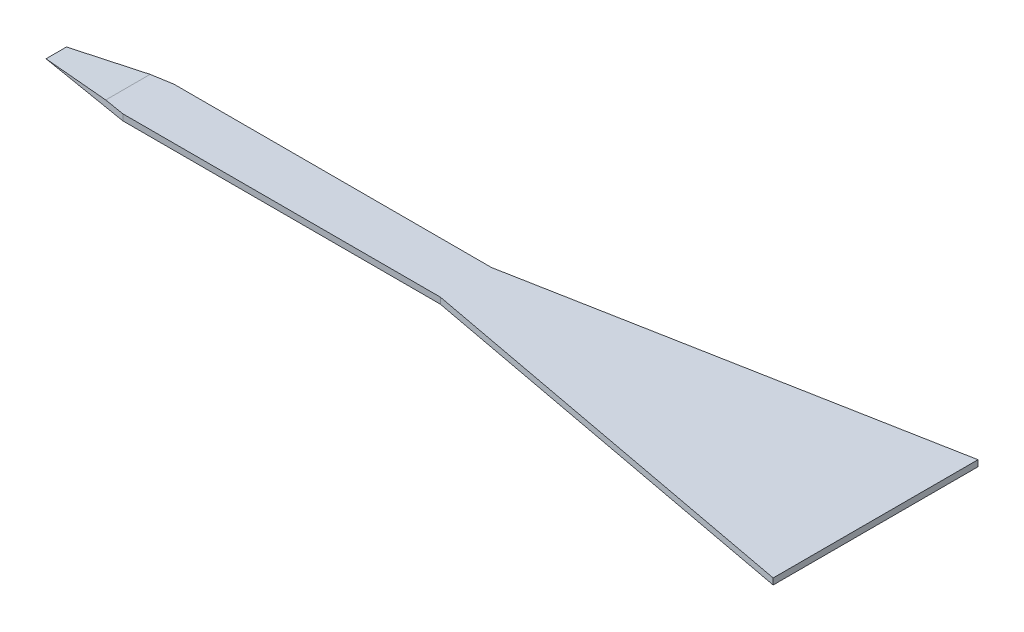
SolidWorks part; units mm, degrees
ref_plane "Front Plane" through (0, 0, 0) normal (0, 0, 1) x (1, 0, 0)
ref_plane "Top Plane" through (0, 0, 0) normal (0, 1, 0) x (1, 0, 0)
ref_plane "Right Plane" through (0, 0, 0) normal (1, 0, 0) x (0, 0, -1)
sketch "Sketch1" plane through (0, 0, 0) normal (0, 1, 0) x (1, 0, 0)
  line L0 (0, 1) -> (0, -1)
  line L1 (-8, -0.25) -> (0, -0.25)
  line L2 (-8, -0.25) -> (-8, 0.25)
  line L3 (0, -0.25) -> (0, 0.25)
  line L4 (-8, 0.25) -> (0, 0.25)
  line L5 (-8, -0.25) -> (0, 0.25) construction
  line L6 (0, -0.25) -> (-8, 0.25) construction
  line L7 (0, 1) -> (-4, 0.25)
  line L8 (0, -1) -> (-4, -0.25)
  line L9 (-4, -0.25) -> (-8, -0.25)
  line L10 (-8, 0.25) -> (-4, 0.25)
  arc A0 (0, 1) -> (0, -1) centre (0, 0) ccw
  point P4 (-1, 0)
  point P6 (-4, 0)
  dimension "D1" = 2
  dimension "D2" = 1
  dimension "D3" = 8
  dimension "D4" = 0.5
extrude "Boss-Extrude1" add sketch "Sketch1" along normal blind 0.06 contours A0 L1 L8 | A0 L7 L4 | A0 L4 L2 L1 | L1 A0 L8 L0 | L7 A0 L4 L0 | L4 A0 L1 L0
sketch "Sketch5" plane through (0, 0, 0.25) normal (0, 0, 1) x (1, 0, 0)
  line L0 (-8, 0) -> (-8, 0.06)
  line L1 (-8, 0.06) -> (-7.3, 0.06)
  line L2 (-8, 0.06) -> (-4, 0.06) construction
  line L3 (-7.3, 0.06) -> (-8, 0)
  dimension "D1" = 0.7
extrude "Cut-Extrude3" cut sketch "Sketch5" against normal through all contours L3 L0 L1
sketch3d "3DSketch1"
  line L0 (-7.3, 0.06, -0.25) -> (-7.3, 0.06, 0.25)
  line L4 (-8, 0.06, 0.25) -> (-8, 0.06, 0.1)
  line L8 (-8, 0.06, 0.1) -> (-7.1, 0.06, 0.25)
  line L9 (-7.1, 0.06, 0.25) -> (-8, 0.06, 0.25)
  line L10 (0, 0.06, -1) -> (0, 0.06, 1) construction
  line L11 (-7.3, 0.06, 0.25) -> (-4, 0.06, 0.25) construction
  line L13 (-8, 0, 0) -> (-7.2904, 0, 0) construction
  line L14 (-8, 0, 0.25) -> (-8, 0, -0.25) construction
  line L15 (-7.1, 0.06, -0.25) -> (-8, 0.06, -0.25)
  line L16 (-8, 0.06, -0.1) -> (-7.1, 0.06, -0.25)
  line L17 (-8, 0.06, -0.25) -> (-8, 0.06, -0.1)
  dimension "D1" = 0.15
  dimension "D2" = 8
  dimension "D3" = 0.9
extrude "Cut-Extrude4" cut sketch "3DSketch1" along direction (0, 1, 0) on the side against the normal through all contours L15 L17 L16 | L8 L9 L4
